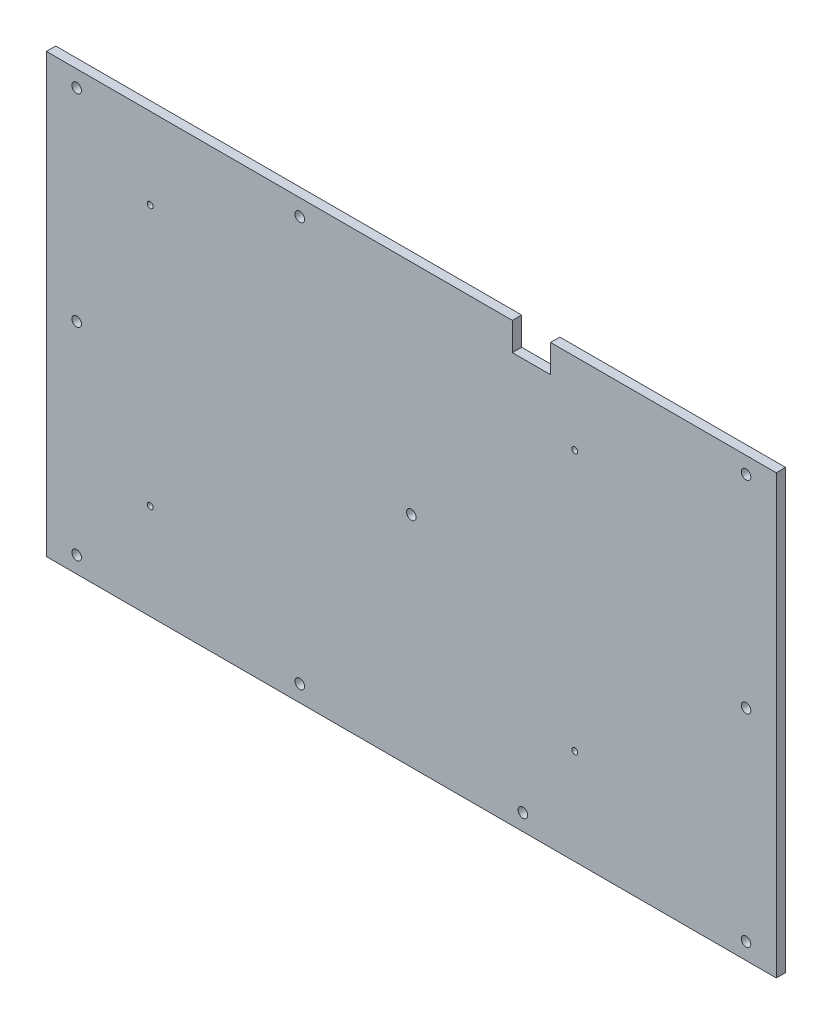
SolidWorks part; units mm, degrees
ref_plane "Front Plane" through (0, 0, 0) normal (0, 0, 1) x (1, 0, 0)
ref_plane "Top Plane" through (0, 0, 0) normal (0, 1, 0) x (1, 0, 0)
ref_plane "Right Plane" through (0, 0, 0) normal (1, 0, 0) x (0, 0, -1)
sketch "Sketch1" plane through (0, 0, 0) normal (0, 0, 1) x (1, 0, 0)
  line L0 (34.4424, 74.6125) -> (34.4424, 65.0875)
  line L1 (-124.46, 74.6125) -> (124.46, 74.6125)
  line L2 (-124.46, 74.6125) -> (-124.46, -74.6125)
  line L3 (-124.46, -74.6125) -> (124.46, -74.6125)
  line L4 (124.46, 74.6125) -> (124.46, -74.6125)
  line L5 (-124.46, 74.6125) -> (124.46, -74.6125) construction
  line L6 (-124.46, -74.6125) -> (124.46, 74.6125) construction
  line L7 (34.4424, 65.0875) -> (47.4726, 65.0875)
  line L8 (47.4726, 65.0875) -> (47.4726, 74.6125)
  point P0 (0, 0)
  dimension "D1" = 248.92
  dimension "D2" = 149.225
  dimension "D3" = 9.525
extrude "Boss-Extrude1" add sketch "Sketch1" along normal blind 3.175 contours L8 L7 L0 L1 L2 L3 L4
hole_wizard "#4 Clearance Hole1" positions "Sketch3" profile "Sketch2" hole size "#4" standard "ANSI Inch"
sketch "Sketch3" plane through (0, 0, 0) normal (0, 0, -1) x (-1, 0, 0)
  line L1 (114.1476, -68.9864) -> (-114.1476, -68.9864)
  line L2 (114.1476, -68.9864) -> (114.1476, 68.9864)
  line L3 (114.1476, 68.9864) -> (-114.1476, 68.9864)
  line L4 (-114.1476, -68.9864) -> (-114.1476, 68.9864)
  line L5 (114.1476, -68.9864) -> (-114.1476, 68.9864) construction
  line L6 (114.1476, 68.9864) -> (-114.1476, -68.9864) construction
  line L7 (38.0492, -68.9864) -> (38.0492, 68.9864) construction
  line L9 (-38.0492, -68.9864) -> (-38.0492, 68.9864) construction
  point P0 (114.1476, -68.9864)
  point P2 (-114.1476, -68.9864)
  point P4 (-114.1476, 68.9864)
  point P6 (114.1476, 68.9864)
  point P8 (114.1476, 0)
  point P10 (-114.1476, 0)
  point P12 (38.0492, 68.9864)
  point P14 (-38.0492, 68.9864)
  point P16 (-38.0492, -68.9864)
  point P18 (38.0492, -68.9864)
  point P21 (0, 0)
  dimension "D1" = 137.9728
  dimension "D2" = 228.2952
  dimension "D3" = 76.0984
  dimension "D4" = 76.0984
sketch "Sketch2" plane through (-114.1476, -68.9864, 0) normal (1, 0, 0) x (0, 1, 0)
  line L0 (0, 0) -> (0, 57.3686)
  line L1 (0, 57.3686) -> (1.6319, 56.388)
  line L2 (1.6319, 56.388) -> (1.6319, 0)
  line L5 (1.6319, 0) -> (0, 0)
  line L10 (0, 57.3686) -> (-1.632, 56.388) construction
  line L11 (0, -6.35) -> (0, 107.95) construction
  dimension "Hole Dia." = 3.2639
  dimension "Hole Depth" = 56.388
  dimension "Drill Angle" = 118
sketch "Sketch6" plane through (0, 0, 0) normal (0, 0, -1) x (-1, 0, 0)
  line L1 (94.1324, -47.0535) -> (-60.8076, -47.0535)
  line L2 (94.1324, -47.0535) -> (94.1324, 52.0065)
  line L3 (94.1324, 52.0065) -> (-60.8076, 52.0065)
  line L4 (-60.8076, -47.0535) -> (-60.8076, 52.0065)
  line L5 (94.1324, -47.0535) -> (-60.8076, 52.0065) construction
  line L6 (94.1324, 52.0065) -> (-60.8076, -47.0535) construction
  line L10 (-124.46, 74.6125) -> (-124.46, -74.6125) construction
  line L11 (124.46, -74.6125) -> (-124.46, -74.6125) construction
  point P0 (16.6624, 2.4765)
  point P11 (-124.46, -15.7329)
  dimension "D1" = 154.94
  dimension "D2" = 99.06
  dimension "D3" = 27.559
  dimension "D4" = 63.6524
hole_wizard "#4-40 Tapped Hole1" positions "Sketch5" profile "Sketch4" tap size "#4-40" standard "ANSI Inch"
sketch "Sketch5" plane through (0, 0, 0) normal (0, 0, -1) x (-1, 0, 0)
  line L2 (-55.7276, -41.9735) -> (89.0524, -41.9735)
  line L3 (-55.7276, -41.9735) -> (-55.7276, 46.9265)
  line L4 (-55.7276, 46.9265) -> (89.0524, 46.9265)
  line L5 (89.0524, -41.9735) -> (89.0524, 46.9265)
  line L6 (89.0524, -41.9735) -> (-55.7276, 46.9265) construction
  point P0 (-55.7276, -41.9735)
  point P2 (-55.7276, 46.9265)
  point P4 (89.0524, 46.9265)
  point P6 (89.0524, -41.9735)
  dimension "D1" = 144.78
  dimension "D2" = 88.9
sketch "Sketch4" plane through (55.7276, -41.9735, 0) normal (1, 0, 0) x (0, 1, 0)
  line L0 (0, 0) -> (0, 8.2305)
  line L1 (0, 8.2305) -> (1.016, 7.62)
  line L2 (1.016, 7.62) -> (1.016, 0)
  line L5 (1.016, 0) -> (0, 0)
  line L10 (0, 8.2305) -> (-1.016, 7.62) construction
  line L11 (0, -6.35) -> (0, 107.95) construction
  dimension "Tap Drill Dia." = 2.032
  dimension "Tap Drill Depth" = 7.62
  dimension "Drill Angle" = 118
cosmetic thread "Hole Thread1" parameters "D1"=3.175, "D2"=2.8448
cosmetic thread "Hole Thread2" parameters "D1"=3.175, "D2"=2.8448
cosmetic thread "Hole Thread3" parameters "D1"=3.175, "D2"=2.8448
cosmetic thread "Hole Thread4" parameters "D1"=3.175, "D2"=2.8448
